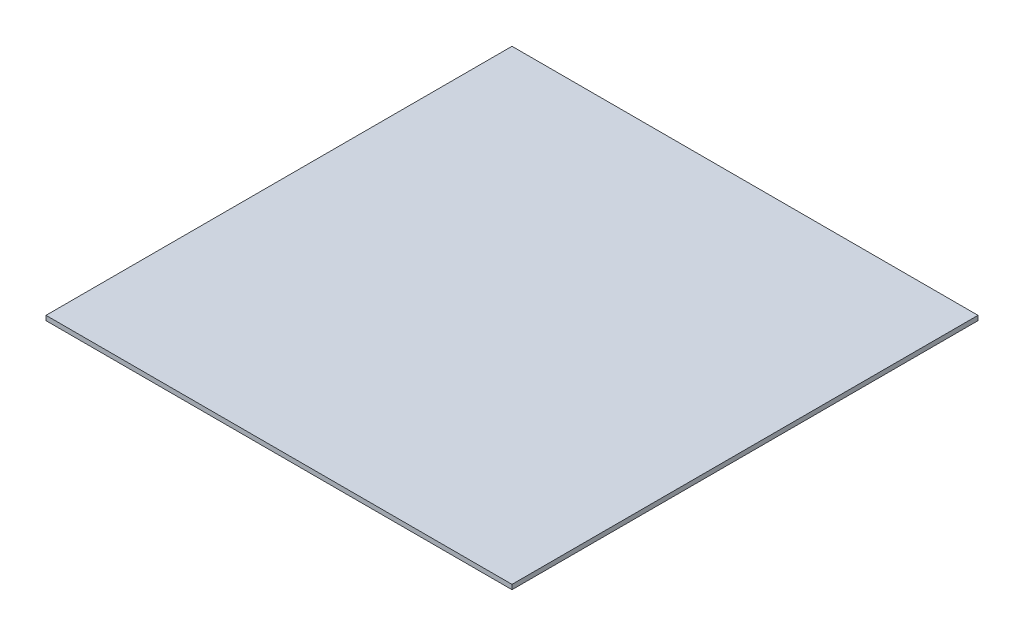
SolidWorks part; units mm, degrees
ref_plane "Front Plane" through (0, 0, 0) normal (0, 0, 1) x (1, 0, 0)
ref_plane "Top Plane" through (0, 0, 0) normal (0, 1, 0) x (1, 0, 0)
ref_plane "Right Plane" through (0, 0, 0) normal (1, 0, 0) x (0, 0, -1)
sketch "Sketch1" plane through (0, 0, 0) normal (0, 1, 0) x (1, 0, 0)
  line L1 (-1270, 1270) -> (1270, 1270)
  line L2 (-1270, 1270) -> (-1270, -1270)
  line L3 (-1270, -1270) -> (1270, -1270)
  line L4 (1270, 1270) -> (1270, -1270)
  line L5 (-1270, 1270) -> (1270, -1270) construction
  line L6 (-1270, -1270) -> (1270, 1270) construction
  point P0 (0, 0)
  dimension "D1" = 2540
  dimension "D2" = 2540
extrude "Boss-Extrude1" add sketch "Sketch1" along normal blind 25.4
